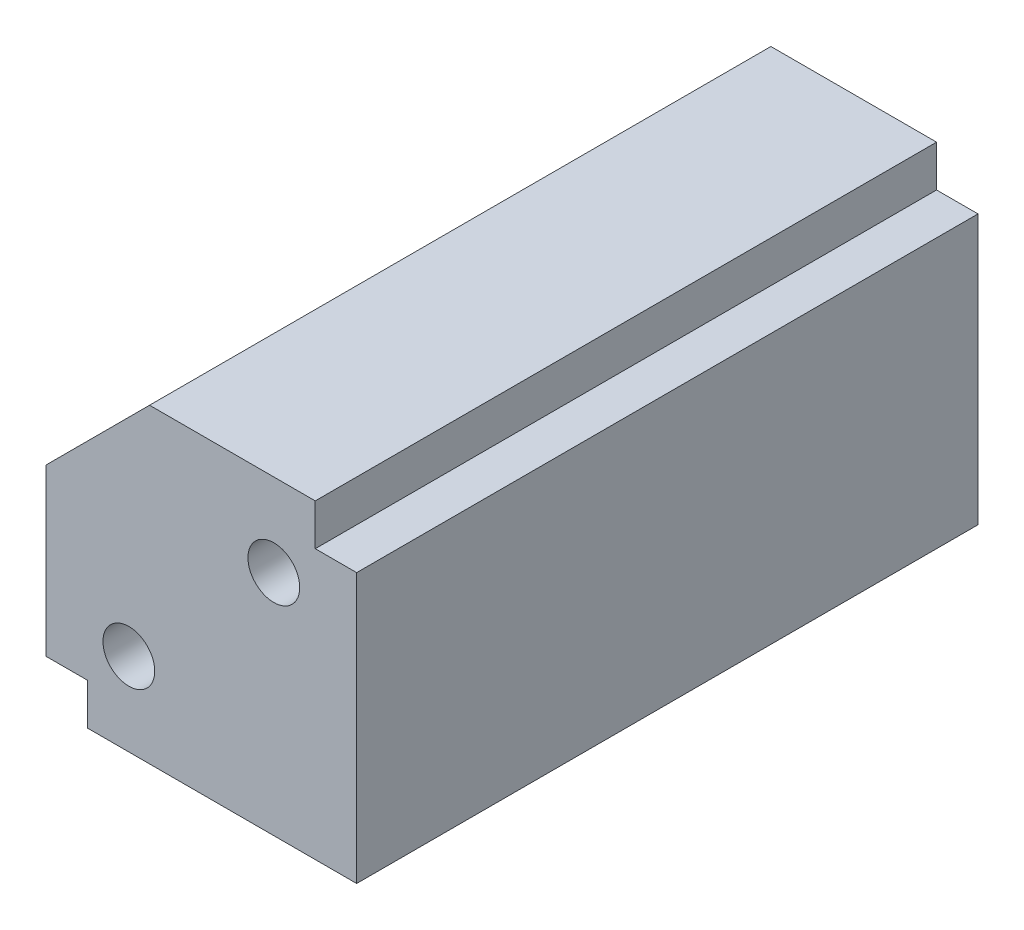
SolidWorks part; units mm, degrees
ref_plane "前视基准面" through (0, 0, 0) normal (0, 0, 1) x (1, 0, 0)
ref_plane "上视基准面" through (0, 0, 0) normal (0, 1, 0) x (1, 0, 0)
ref_plane "右视基准面" through (0, 0, 0) normal (1, 0, 0) x (0, 0, -1)
sketch "草图1" plane through (0, 0, 0) normal (0, 0, 1) x (1, 0, 0)
  line L1 (7.5, -7.5) -> (-7.5, -7.5)
  line L2 (7.5, -7.5) -> (7.5, 7.5)
  line L3 (7.5, 7.5) -> (-7.5, 7.5)
  line L4 (-7.5, -7.5) -> (-7.5, 7.5)
  line L5 (7.5, -7.5) -> (-7.5, 7.5) construction
  line L6 (7.5, 7.5) -> (-7.5, -7.5) construction
  point P0 (0, 0)
  dimension "D1" = 15
  dimension "D2" = 15
extrude "凸台-拉伸1" add sketch "草图1" along normal blind 30
chamfer "倒角1" distance 5 angle 45 1 edges at (-7.5, 7.5, 15)
hole_wizard "M3 螺纹孔2" positions "草图2" profile "草图3" tap size "M3" standard "GB"
sketch "草图2" plane through (0, 0, 30) normal (0, 0, 1) x (1, 0, 0)
  line L5 (-7.5, 2.5) -> (-7.5, -7.5) construction
  line L6 (-7.5, -7.5) -> (7.5, -7.5) construction
  line L7 (7.5, 7.5) -> (-2.5, 7.5) construction
  line L8 (7.5, -7.5) -> (7.5, 7.5) construction
  point P0 (-3.5, -3.5)
  point P2 (3.5, 3.5)
  dimension "D1" = 4
  dimension "D2" = 4
  dimension "D3" = 4
  dimension "D4" = 4
sketch "草图3" plane through (-3.5, -3.5, 30) normal (1, 0, 0) x (0, -1, 0)
  line L0 (0, 0) -> (0, 8.2511)
  line L1 (0, 8.2511) -> (1.25, 7.5)
  line L2 (1.25, 7.5) -> (1.25, 0)
  line L5 (1.25, 0) -> (0, 0)
  line L10 (0, 8.2511) -> (-1.25, 7.5) construction
  line L11 (0, -6.35) -> (0, 107.95) construction
  dimension "螺纹孔钻头直径" = 2.5
  dimension "螺纹孔钻头深度" = 7.5
  dimension "导头角度" = 118
cosmetic thread "孔螺蚊线1" parameters "D1"=6, "D2"=3
cosmetic thread "孔螺蚊线2" parameters "D1"=6, "D2"=3
sketch "草图4" plane through (-5, 5, 0) normal (-0.7071, 0.7071, 0) x (0, 0, 1)
  line L0 (15, 3.5355) -> (15, -3.5355) construction
  line L1 (0, 3.5355) -> (30, 3.5355) construction
  line L2 (30, -3.5355) -> (0, -3.5355) construction
ref_plane "基准面1" through (0, 0, 15) normal (0, 0, -1) x (-0.7071, -0.7071, 0)
mirror "镜向1" about plane through (0, 0, 15) normal (0, 0, -1) of "M3 螺纹孔2"
sketch "草图5" plane through (0, 7.5, 0) normal (0, 1, 0) x (1, 0, 0)
  line L0 (7.5, -30) -> (-2.5, -30) construction
  line L1 (7.5, 0) -> (5.5, 0)
  line L2 (7.5, 0) -> (7.5, -30)
  line L3 (7.5, -30) -> (5.5, -30)
  line L4 (5.5, 0) -> (5.5, -30)
  dimension "D1" = 2
extrude "切除-拉伸1" cut sketch "草图5" against normal blind 2
sketch "草图6" plane through (-7.5, 0, 0) normal (-1, 0, 0) x (0, 0, 1)
  line L0 (30, 2.5) -> (30, -7.5) construction
  line L1 (0, -7.5) -> (30, -7.5)
  line L2 (0, -7.5) -> (0, -5.5)
  line L3 (0, -5.5) -> (30, -5.5)
  line L4 (30, -7.5) -> (30, -5.5)
  dimension "D1" = 2
extrude "切除-拉伸2" cut sketch "草图6" against normal blind 2
